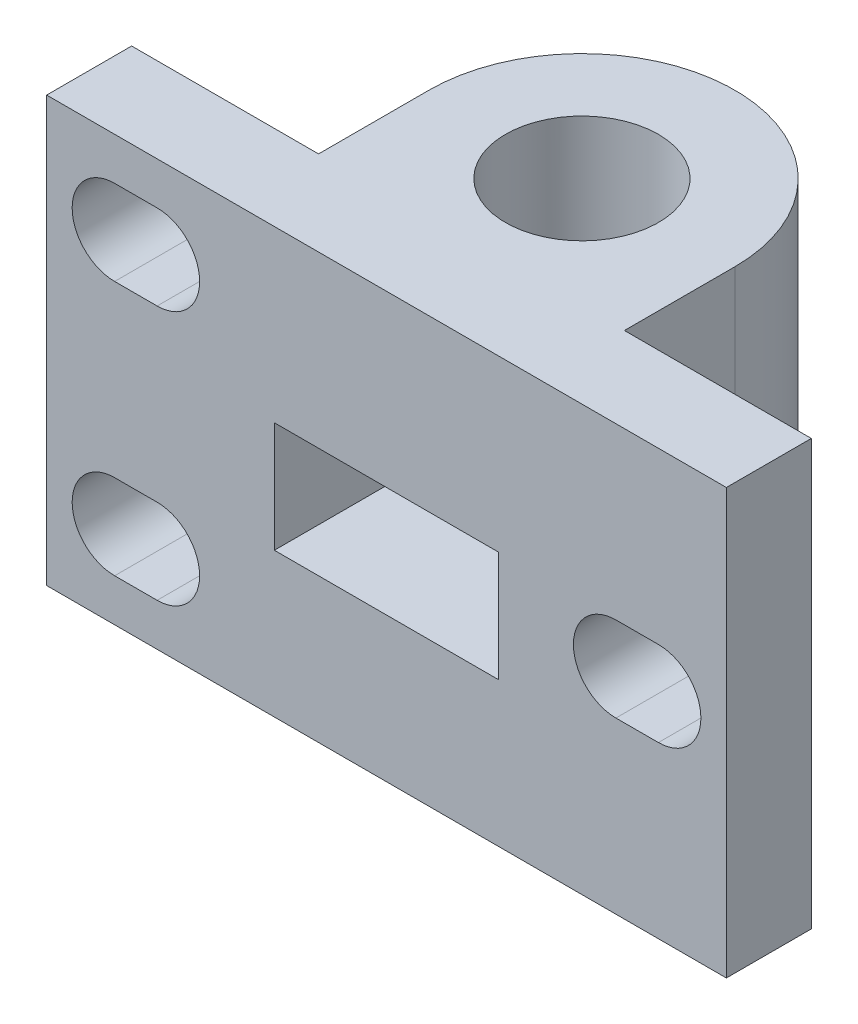
SolidWorks part; units mm, degrees
material "Copper"
ref_plane "Front Plane" through (0, 0, 0) normal (0, 0, 1) x (1, 0, 0)
ref_plane "Top Plane" through (0, 0, 0) normal (0, 1, 0) x (1, 0, 0)
ref_plane "Right Plane" through (0, 0, 0) normal (1, 0, 0) x (0, 0, -1)
sketch "Sketch1" plane through (0, 0, 0) normal (0, 1, 0) x (1, 0, 0)
  line L0 (0, 0) -> (0, 49.18) construction
  line L1 (20, 0) -> (-20, 0)
  line L2 (-20, 0) -> (-20, 5)
  line L3 (-9, 11.5) -> (-9, 5)
  line L4 (-9, 5) -> (-20, 5)
  line L5 (9, 5) -> (20, 5)
  line L6 (9, 11.5) -> (9, 5)
  line L7 (20, 0) -> (20, 5)
  circle A0 centre (0, 11.5) radius 4.5
  arc A1 (9, 11.5) -> (-9, 11.5) centre (0, 11.5) ccw
  dimension "D2" = 20
  dimension "D1" = 11.5
  dimension "D3" = 9
  dimension "D4" = 9
extrude "Boss-Extrude1" add sketch "Sketch1" along normal blind 25
ref_plane "Plane1" through (0, 15, 0) normal (0, 1, 0) x (1, 0, 0)
sketch "Sketch2" plane through (0, 15, 0) normal (0, 1, 0) x (1, 0, 0)
  line L1 (0, 19.121) -> (-6.6, 15.3105)
  line L2 (-6.6, 15.3105) -> (-6.6, 7.6895)
  line L3 (-6.6, 7.6895) -> (0, 3.879)
  line L4 (0, 3.879) -> (6.6, 7.6895)
  line L5 (6.6, 7.6895) -> (6.6, 15.3105)
  line L6 (6.6, 15.3105) -> (0, 19.121)
  circle A0 centre (0, 11.5) radius 6.6 construction
extrude "Cut-Extrude1" cut sketch "Sketch2" against normal blind 6.5
ref_plane "Plane2" through (0, 0, -7.6895) normal (0, 0, -1) x (-1, 0, 0)
sketch "Sketch4" plane through (0, 0, -7.6895) normal (0, 0, -1) x (-1, 0, 0)
  line L0 (6.6, 8.5) -> (6.6, 15) construction
  line L1 (6.6, 15) -> (-6.6, 15)
  line L2 (6.6, 15) -> (6.6, 8.5)
  line L3 (6.6, 8.5) -> (-6.6, 8.5)
  line L4 (-6.6, 15) -> (-6.6, 8.5)
  line L5 (-6.6, 8.5) -> (-6.6, 15) construction
extrude "Cut-Extrude2" cut sketch "Sketch4" against normal through all
sketch "Sketch5" plane through (0, 0, -5) normal (0, 0, -1) x (-1, 0, 0)
  line L0 (-16, 12.5) -> (-13.5, 12.5) construction
  line L1 (-20, 25) -> (-9, 25) construction
  line L2 (-16, 15) -> (-13.5, 15)
  line L3 (-16, 10) -> (-13.5, 10)
  line L4 (-20, 25) -> (-20, 0) construction
  line L5 (13.5, 20) -> (16, 20) construction
  line L6 (13.5, 22.5) -> (16, 22.5)
  line L7 (13.5, 17.5) -> (16, 17.5)
  line L8 (13.5, 5) -> (16, 5) construction
  line L9 (13.5, 7.5) -> (16, 7.5)
  line L10 (13.5, 2.5) -> (16, 2.5)
  line L11 (20, 25) -> (20, 0) construction
  line L12 (9, 25) -> (20, 25) construction
  line L13 (9, 0) -> (20, 0) construction
  arc A0 (-16, 15) -> (-16, 10) centre (-16, 12.5) ccw
  arc A1 (-13.5, 10) -> (-13.5, 15) centre (-13.5, 12.5) ccw
  arc A2 (13.5, 22.5) -> (13.5, 17.5) centre (13.5, 20) ccw
  arc A3 (16, 17.5) -> (16, 22.5) centre (16, 20) ccw
  arc A4 (13.5, 7.5) -> (13.5, 2.5) centre (13.5, 5) ccw
  arc A5 (16, 2.5) -> (16, 7.5) centre (16, 5) ccw
  point P4 (-14.75, 12.5)
  point P13 (14.75, 20)
  point P20 (14.75, 5)
  dimension "D1" = 12.5
  dimension "D2" = 4
  dimension "D3" = 2.5
  dimension "D4" = 2.5
  dimension "D5" = 4
  dimension "D6" = 5
  dimension "D7" = 2.5
  dimension "D8" = 4
  dimension "D9" = 5
extrude "Cut-Extrude3" cut sketch "Sketch5" against normal through all
